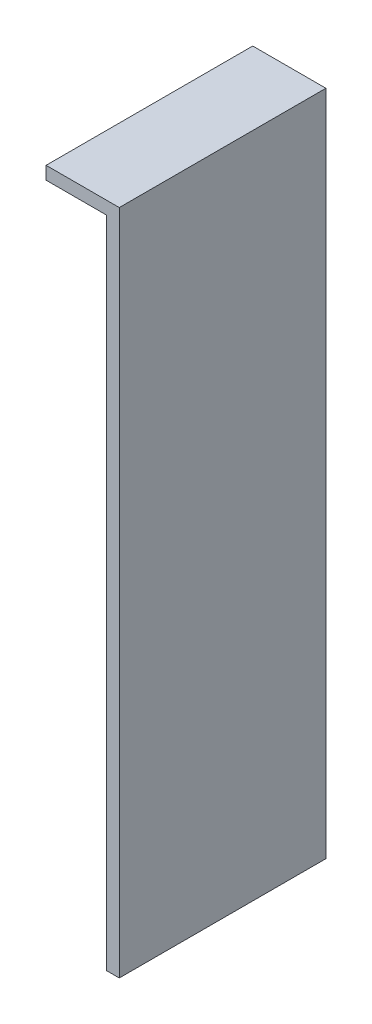
SolidWorks part; units mm, degrees
ref_plane "Front Plane" through (0, 0, 0) normal (0, 0, 1) x (1, 0, 0)
ref_plane "Top Plane" through (0, 0, 0) normal (0, 1, 0) x (1, 0, 0)
ref_plane "Right Plane" through (0, 0, 0) normal (1, 0, 0) x (0, 0, -1)
sketch "Sketch1" plane through (0, 0, 0) normal (0, 0, 1) x (1, 0, 0)
  line L0 (0, 0) -> (2605.2992, 0) construction
  line L1 (0, 0) -> (0, -2605.2992) construction
  line L3 (-2.125, 19.375) -> (2.125, 19.375)
  line L4 (-2.125, 19.375) -> (-2.125, -19.375)
  line L5 (-2.125, -19.375) -> (2.125, -19.375)
  line L6 (2.125, 19.375) -> (2.125, -19.375)
  point P9 (0, 19.375)
  point P10 (2.125, 0)
  dimension "D1" = 4.25
  dimension "D2" = 38.75
extrude "Boss-Extrude1" add sketch "Sketch1" along normal blind 12
sketch "Sketch2" plane through (-2.125, 0, 0) normal (-1, 0, 0) x (0, 0, 1)
  line L0 (12, 19.375) -> (0, 19.375) construction
  line L1 (12, -19.375) -> (2.25, -19.375)
  line L2 (12, -19.375) -> (12, 18.625)
  line L3 (12, 18.625) -> (2.25, 18.625)
  line L4 (2.25, -19.375) -> (2.25, 18.625)
  line L5 (0, 19.375) -> (0, -19.375) construction
  dimension "D1" = 0.75
  dimension "D2" = 2.25
extrude "Cut-Extrude1" cut sketch "Sketch2" against normal blind 3.5
ref_plane "Plane1" through (-12.125, 0, 0) normal (-1, 0, 0) x (0, 0, 1)
